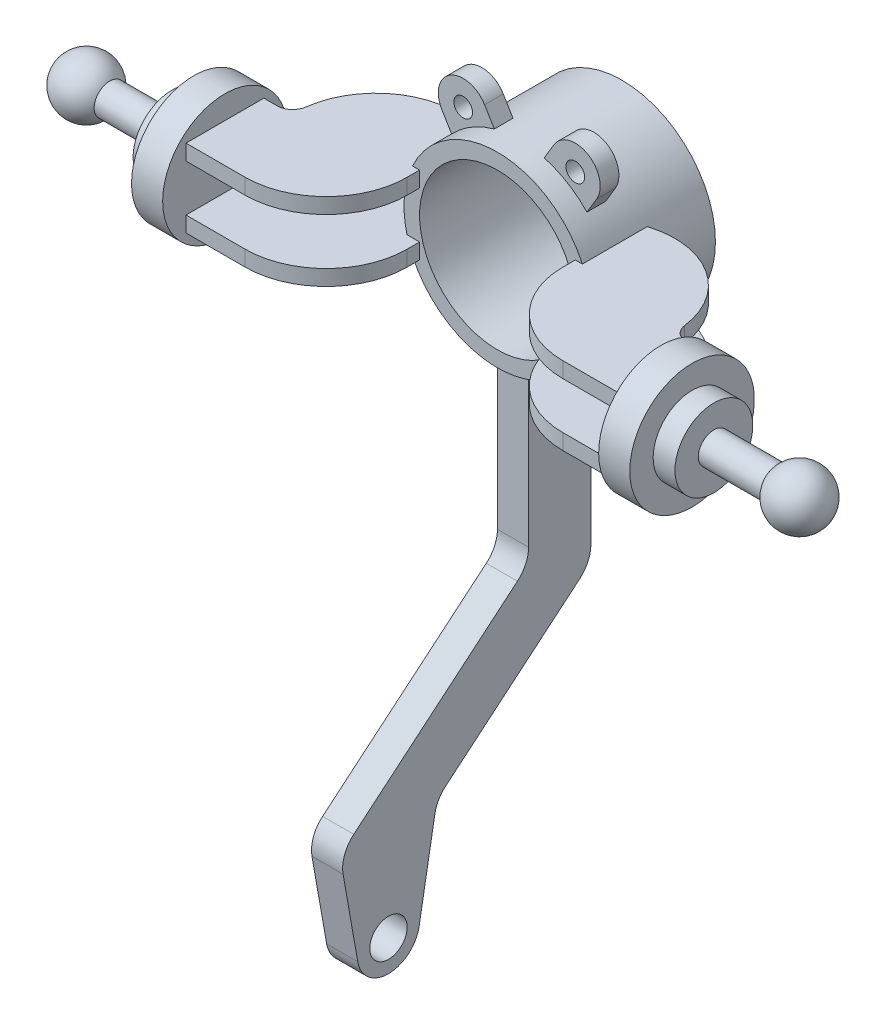
SolidWorks part; units mm, degrees
material "Plain Carbon Steel"
ref_plane "Front Plane" through (0, 0, 0) normal (0, 0, 1) x (1, 0, 0)
ref_plane "Top Plane" through (0, 0, 0) normal (0, 1, 0) x (1, 0, 0)
ref_plane "Right Plane" through (0, 0, 0) normal (1, 0, 0) x (0, 0, -1)
sketch "Sketch1" plane through (0, 0, 0) normal (0, 0, 1) x (1, 0, 0)
  circle A0 centre (0, 0) radius 30
  dimension "D2" = 60
extrude "Boss-Extrude1" add sketch "Sketch1" along normal mid plane 40
sketch "Sketch2" plane through (0, 0, 0) normal (1, 0, 0) x (0, 0, -1)
  line L1 (-15, 0) -> (5, 0)
  line L8 (20, -30) -> (20, 30) construction
  line L13 (-15, 0) -> (-15, -79.8816)
  line L14 (-18.5721, -87.542) -> (-71.1345, -131.6471)
  line L15 (-74.5547, -141.044) -> (-69.8481, -167.7365)
  line L16 (-50.1519, -167.7365) -> (-45.0748, -138.9426)
  line L17 (-41.6546, -133.0187) -> (1.4279, -96.8682)
  line L18 (5, -89.2077) -> (5, 0)
  arc A5 (-69.8481, -167.7365) -> (-50.1519, -167.7365) centre (-60, -166) ccw
  arc A6 (-15, -79.8816) -> (-18.5721, -87.542) centre (-25, -79.8816) cw
  arc A7 (1.4279, -96.8682) -> (5, -89.2077) centre (-5, -89.2077) ccw
  arc A8 (-45.0748, -138.9426) -> (-41.6546, -133.0187) centre (-35.2267, -140.6791) cw
  arc A9 (-71.1345, -131.6471) -> (-74.5547, -141.044) centre (-64.7066, -139.3075) ccw
  circle A10 centre (-60, -166) radius 6
  point P17 (-15, -84.5447)
  point P22 (-44.4428, -135.3582)
  point P23 (77.7614, -96.4451)
  point P26 (-75.5572, -135.3582)
  dimension "D1" = 20
  dimension "D8" = 20
  dimension "D9" = 60
  dimension "D10" = 10
  dimension "D11" = 12
  dimension "D3" = 10
  dimension "D2" = 15
  dimension "D4" = 20
  dimension "D5" = 166
  dimension "D6" = 130
  dimension "D7" = 120
extrude "Boss-Extrude2" add sketch "Sketch2" along normal mid plane 10 contours A9
ref_plane "Plane1" through (0, -10, 0) normal (0, 1, 0) x (1, 0, 0)
sketch "Sketch5" plane through (0, -10, 10) normal (0, 1, 0) x (1, 0, 0)
  line L1 (60.9808, -15) -> (70, -15)
  line L5 (25, 10) -> (25, -14)
  line L6 (70, -15) -> (70, -40)
  line L7 (70, -40) -> (51, -40)
  arc A2 (51, -40) -> (25, -14) centre (51, -14) cw
  arc A3 (25, 10) -> (60.9808, -15) centre (35, -14) cw
  dimension "D1" = 26
  dimension "D2" = 70
  dimension "D4" = 70
  dimension "D3" = 25
  dimension "D5" = 25
extrude "Boss-Extrude3" add sketch "Sketch5" along normal mid plane 5
mirror "Mirror1" about plane through (0, 0, 0) normal (0, 1, 0) of "Boss-Extrude3"
sketch "Sketch7" plane through (0, 0, 0) normal (0, -1, 0) x (1, 0, 0)
  line L0 (70, 37.5) -> (132.6236, 37.5) construction
  line L1 (70, 17.5) -> (80, 17.5)
  line L2 (80, 17.5) -> (80, 25)
  line L3 (80, 25) -> (87, 25)
  line L4 (87, 25) -> (87, 32.5)
  line L5 (87, 32.5) -> (107, 32.5)
  line L6 (70, 50) -> (70, 25) construction
  line L10 (70, 37.5) -> (70, 17.5)
  line L11 (123.4833, 37.5) -> (70, 37.5)
  arc A0 (107, 32.5) -> (123.4833, 37.5) centre (114.4833, 37.5) ccw
  dimension "D6" = 9
  dimension "D1" = 40
  dimension "D2" = 25
  dimension "D3" = 10
  dimension "D4" = 7
  dimension "D5" = 20
  dimension "D7" = 10
revolve "Revolve1" add sketch "Sketch7" angle 360 about L0
ref_plane "Plane3" through (0, 0, 10) normal (0, 0, 1) x (1, 0, 0)
sketch "Sketch8" plane through (0, 0, 10) normal (0, 0, 1) x (1, 0, 0)
  line L0 (0, 0) -> (28.3567, 47.2612) construction
  line L1 (0, 0) -> (37.169, 0) construction
  line L2 (24.8599, 25.884) -> (21.7359, 20.6773)
  line L3 (11.1401, 34.116) -> (8.016, 28.9092)
  line L4 (0, 0) -> (0, 34.116) construction
  arc A0 (24.8599, 25.884) -> (11.1401, 34.116) centre (18, 30) ccw
  arc A1 (8.016, 28.9092) -> (21.7359, 20.6773) centre (0, 0) cw
  arc A2 (27.2718, 12.5) -> (27.2718, -12.5) centre (0, 0) ccw construction
  circle A3 centre (18, 30) radius 3
  dimension "D2" = 8
  dimension "D4" = 6
  dimension "D1" = 30
  dimension "D3" = 36
extrude "Boss-Extrude4" add sketch "Sketch8" along normal mid plane 6
mirror "Mirror2" about plane through (0, 0, 0) normal (1, 0, 0) of "Boss-Extrude4", "Revolve1", "Mirror1", "Boss-Extrude3"
sketch "Sketch3" plane through (0, 0, 20) normal (0, 0, 1) x (1, 0, 0)
  circle A0 centre (0, 0) radius 25
  dimension "D1" = 50
extrude "Cut-Extrude1" cut sketch "Sketch3" against normal through all both and the other way through all
fillet "Fillet1" radius 5 4 edges at (60.9808, -10, 25) (60.9808, 10, 25) (-60.9808, -10, 25) (-60.9808, 10, 25)
